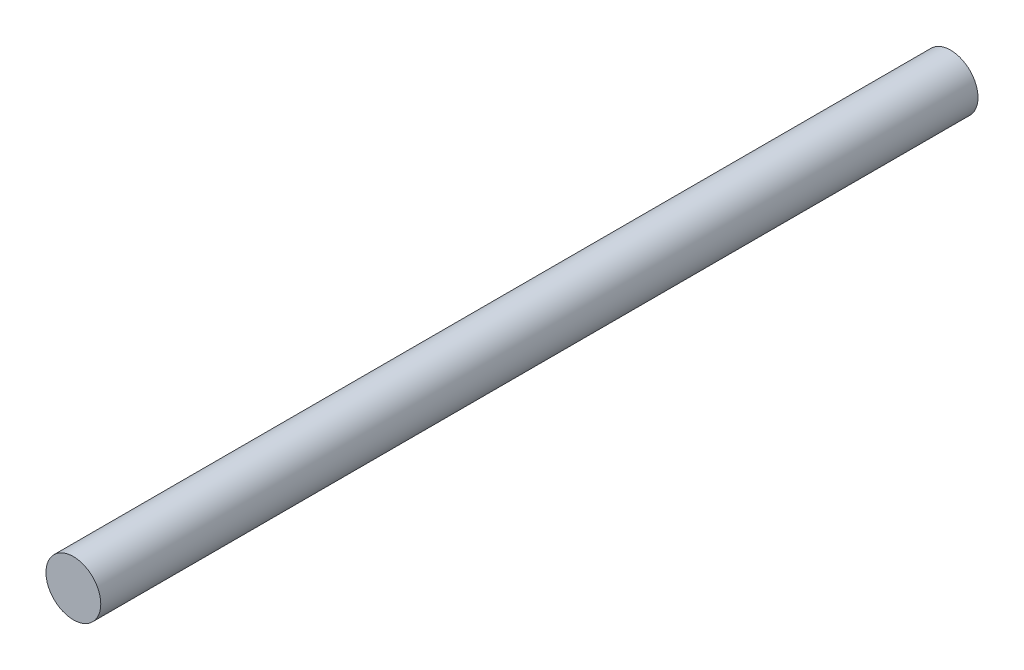
SolidWorks part; units mm, degrees
ref_plane "Front Plane" through (0, 0, 0) normal (0, 0, 1) x (1, 0, 0)
ref_plane "Top Plane" through (0, 0, 0) normal (0, 1, 0) x (1, 0, 0)
ref_plane "Right Plane" through (0, 0, 0) normal (1, 0, 0) x (0, 0, -1)
sketch "Sketch1" plane through (0, 0, 0) normal (0, 0, 1) x (1, 0, 0)
  circle A0 centre (0, 0) radius 0.635
  dimension "D1" = 1.27
extrude "Boss-Extrude1" add sketch "Sketch1" along normal blind 20.32
sketch "Sketch3" plane through (0, 0, 20.32) normal (0, 0, 1) x (1, 0, 0)
  circle A1 centre (0, 0) radius 0.635
curve "Helix/Spiral1" pitch 27.94 height 20.32 turns 0.7273
